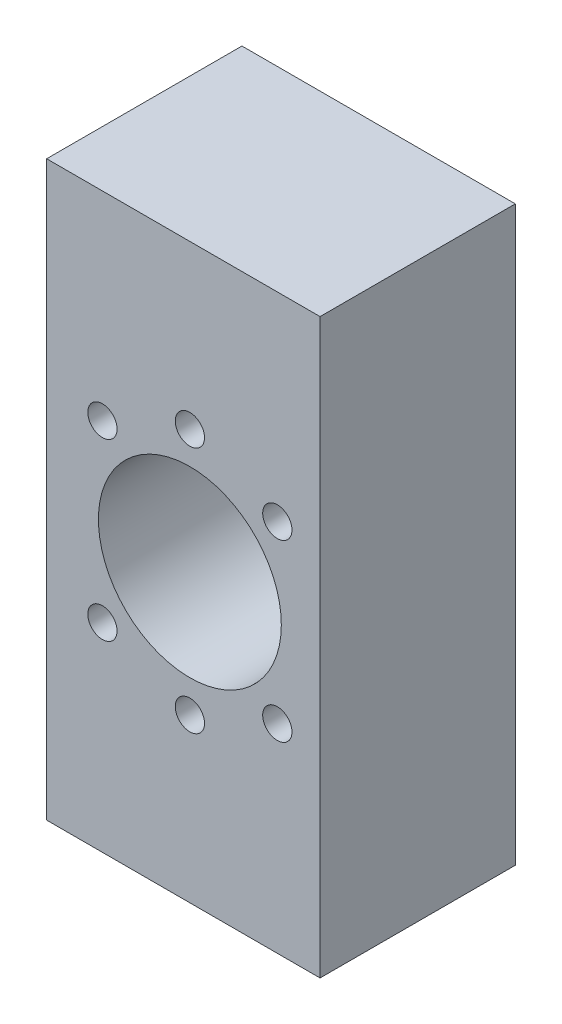
SolidWorks part; units mm, degrees
material "7079 Alloy"
ref_plane "Front" through (0, 0, 0) normal (0, 0, 1) x (1, 0, 0)
ref_plane "Top" through (0, 0, 0) normal (0, 1, 0) x (1, 0, 0)
ref_plane "Right" through (0, 0, 0) normal (1, 0, 0) x (0, 0, -1)
sketch "Sketch1" plane through (0, 0, 0) normal (0, 0, 1) x (1, 0, 0)
  line L0 (-20, 44) -> (-22, 44)
  line L1 (20, 44) -> (20, -44)
  line L2 (20, 44) -> (-20, 44)
  line L4 (-22, 44) -> (-22, -44)
  line L5 (-22, -44) -> (-20, -44)
  line L24 (-20, 44) -> (20, 44)
  line L28 (-20, -44) -> (20, -44)
  circle A1 centre (0, 0) radius 14.05
  circle A3 centre (-13.435, 13.435) radius 2.25
  circle A4 centre (0, 19) radius 2.25
  circle A5 centre (13.435, 13.435) radius 2.25
  circle A6 centre (13.435, -13.435) radius 2.25
  circle A7 centre (0, -19) radius 2.25
  circle A8 centre (-13.435, -13.435) radius 2.25
extrude "Extrude7" add sketch "Sketch1" along normal blind 30 from offset 10
sketch "Sketch8" plane through (-20, 0, 0) normal (-1, 0, 0) x (0, 0, 1)
  circle A0 centre (17.5, 39) radius 2.25
  circle A1 centre (32.5, 39) radius 2.25
  circle A2 centre (17.5, -39) radius 2.25
  circle A3 centre (32.5, -39) radius 2.25
  circle A4 centre (17.5, 29) radius 2.25
  circle A5 centre (32.5, 29) radius 2.25
  circle A6 centre (17.5, -29) radius 2.25
  circle A7 centre (32.5, -29) radius 2.25
extrude "Cut-Extrude6" cut sketch "Sketch8" against normal blind 30 from offset 2
